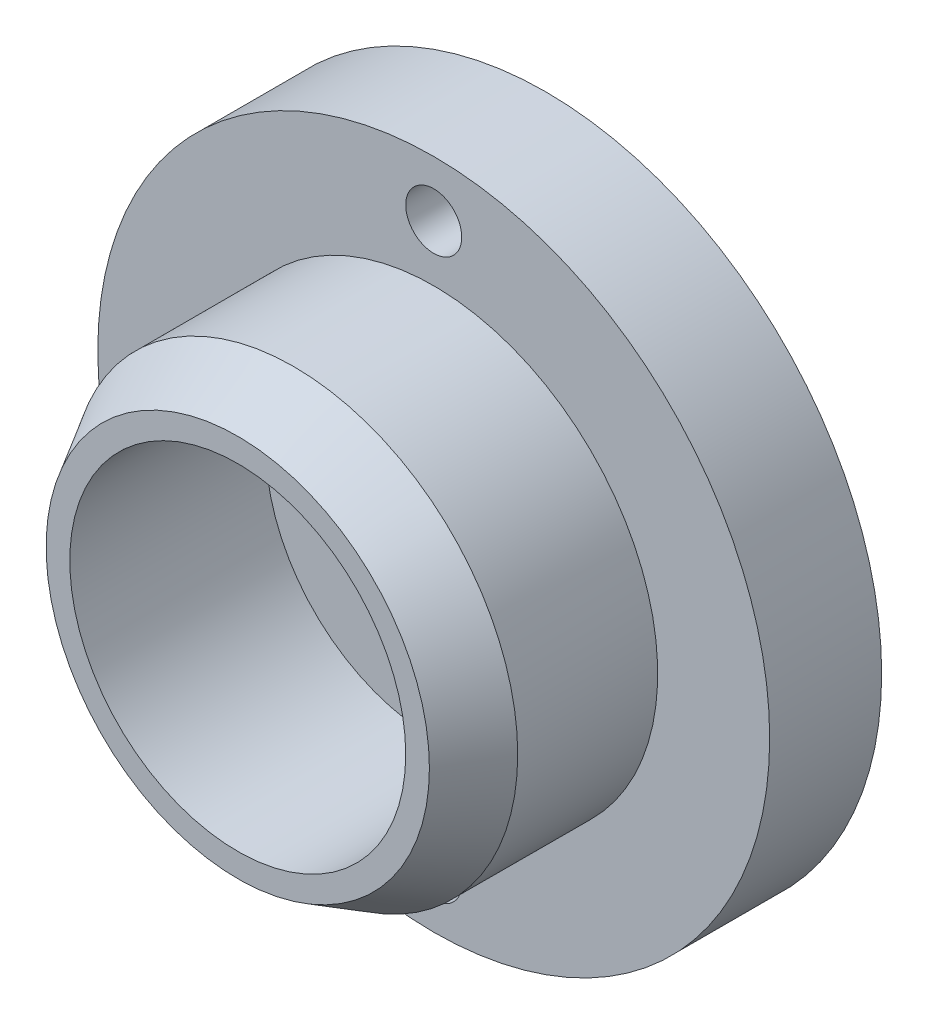
SolidWorks part; units mm, degrees
ref_plane "Front Plane" through (0, 0, 0) normal (0, 0, 1) x (1, 0, 0)
ref_plane "Top Plane" through (0, 0, 0) normal (0, 1, 0) x (1, 0, 0)
ref_plane "Right Plane" through (0, 0, 0) normal (1, 0, 0) x (0, 0, -1)
sketch "Sketch1" plane through (0, 0, 0) normal (0, 0, 1) x (1, 0, 0)
  circle A0 centre (0, 0) radius 3
  circle A1 centre (0, 0) radius 4
  dimension "D1" = 6
  dimension "D2" = 8
extrude "Boss-Extrude1" add sketch "Sketch1" along normal blind 3.5
chamfer "Chamfer1" distance 1 angle 30 1 edges at (4, 0, 3.5)
sketch "Sketch2" plane through (0, 0, 0) normal (0, 0, -1) x (-1, 0, 0)
  circle A0 centre (0, 0) radius 6
  dimension "D1" = 12
extrude "Boss-Extrude2" add sketch "Sketch2" along normal blind 2
sketch "Sketch3" plane through (0, 0, 0) normal (0, 0, 1) x (1, 0, 0)
  line L0 (0, 6) -> (0, -6) construction
  circle A0 centre (0, 0) radius 6 construction
  circle A1 centre (0, 5) radius 0.5
  circle A2 centre (0, -5) radius 0.5
  dimension "D1" = 1
  dimension "D2" = 1
  dimension "D3" = 1
extrude "Cut-Extrude1" cut sketch "Sketch3" against normal up to surface (2 mm away) up to face at (-6, 0, -2)
